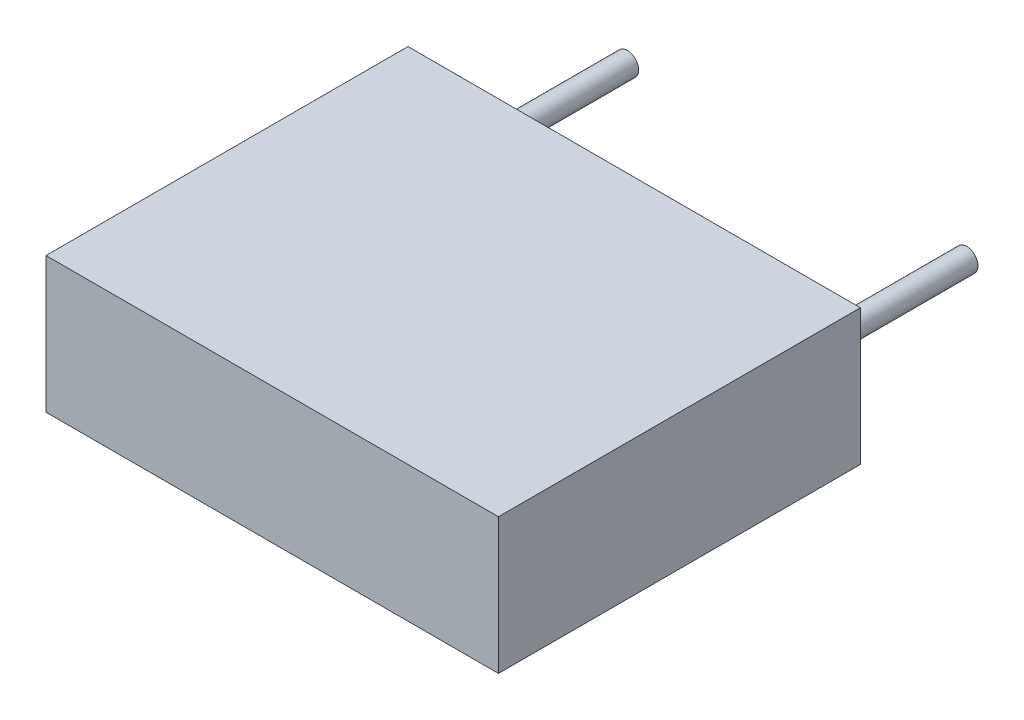
SolidWorks part; units mm, degrees
ref_plane "Plan de face" through (0, 0, 0) normal (0, 0, 1) x (1, 0, 0)
ref_plane "Plan de dessus" through (0, 0, 0) normal (0, 1, 0) x (1, 0, 0)
ref_plane "Plan de droite" through (0, 0, 0) normal (1, 0, 0) x (0, 0, -1)
sketch "Esquisse1" plane through (0, 0, 0) normal (0, 0, 1) x (1, 0, 0)
  line L1 (-5, -1.5) -> (5, -1.5)
  line L2 (-5, -1.5) -> (-5, 1.5)
  line L3 (-5, 1.5) -> (5, 1.5)
  line L4 (5, -1.5) -> (5, 1.5)
  line L5 (-5, -1.5) -> (5, 1.5) construction
  line L6 (-5, 1.5) -> (5, -1.5) construction
  point P0 (0, 0)
  dimension "D1" = 3
  dimension "D2" = 10
extrude "Boss.-Extru.1" add sketch "Esquisse1" along normal blind 8
sketch "Esquisse2" plane through (0, 0, 0) normal (0, 0, -1) x (-1, 0, 0)
  line L0 (-3.75, 0) -> (0, 0) construction
  line L1 (0, 0) -> (3.75, 0) construction
  circle A0 centre (-3.75, 0) radius 0.25
  circle A1 centre (3.75, 0) radius 0.25
  dimension "D1" = 0.5
  dimension "D2" = 7.5
extrude "Boss.-Extru.2" add sketch "Esquisse2" along normal blind 3.6
